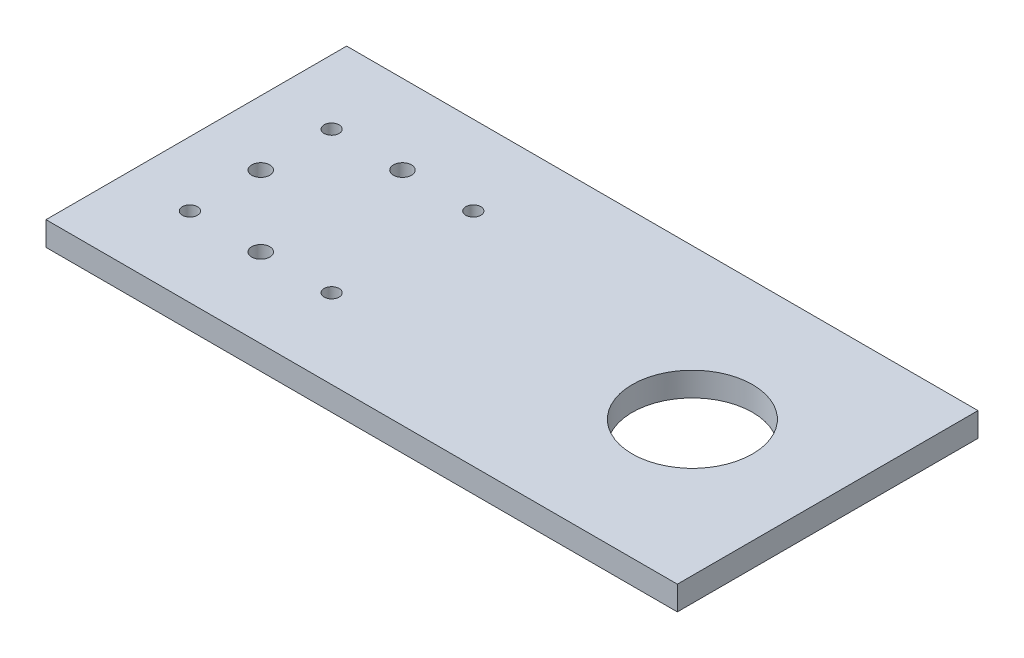
SolidWorks part; units mm, degrees
ref_plane "Front Plane" through (0, 0, 0) normal (0, 0, 1) x (1, 0, 0)
ref_plane "Top Plane" through (0, 0, 0) normal (0, 1, 0) x (1, 0, 0)
ref_plane "Right Plane" through (0, 0, 0) normal (1, 0, 0) x (0, 0, -1)
sketch "Sketch1" plane through (0, 0, 0) normal (0, 1, 0) x (1, 0, 0)
  line L1 (-125, 50) -> (125, 50)
  line L2 (-125, 50) -> (-125, -50)
  line L3 (-125, -50) -> (125, -50)
  line L4 (125, 50) -> (125, -50)
  line L5 (-125, 50) -> (125, -50) construction
  line L6 (-125, -50) -> (125, 50) construction
  point P0 (0, 0)
  dimension "D1" = 100
  dimension "D2" = 250
extrude "Boss-Extrude1" add sketch "Sketch1" along normal blind 8
sketch "Sketch2" plane through (0, 8, 0) normal (0, 1, 0) x (1, 0, 0)
  line L0 (-125, -50) -> (-80, -50)
  line L1 (-125, -50) -> (125, -50) construction
  line L2 (-80, -50) -> (-80, 50)
  line L4 (-116, 36) -> (-44, 36)
  line L5 (-110, 30) -> (-50, 30)
  line L6 (-110, 30) -> (-110, -30)
  line L7 (-110, -30) -> (-50, -30)
  line L8 (-50, 30) -> (-50, -30)
  line L9 (-110, 30) -> (-50, -30) construction
  line L10 (-110, -30) -> (-50, 30) construction
  line L11 (-103.57, 23.57) -> (-56.43, 23.57)
  line L12 (-103.57, 23.57) -> (-103.57, -23.57)
  line L13 (-103.57, -23.57) -> (-56.43, -23.57)
  line L14 (-56.43, 23.57) -> (-56.43, -23.57)
  line L15 (-103.57, 23.57) -> (-56.43, -23.57) construction
  line L16 (-103.57, -23.57) -> (-56.43, 23.57) construction
  line L17 (-116, 36) -> (-116, -36)
  line L18 (-116, -36) -> (-44, -36)
  line L19 (-44, 36) -> (-44, -36)
  line L20 (-116, 36) -> (-44, -36) construction
  line L21 (-116, -36) -> (-44, 36) construction
  circle A0 centre (-80, 0) radius 4
  circle A1 centre (-103.57, 23.57) radius 2.5
  circle A2 centre (-56.43, 23.57) radius 2.5
  circle A3 centre (-56.43, -23.57) radius 2.5
  circle A4 centre (-103.57, -23.57) radius 2.5
  circle A5 centre (-80, 0) radius 19.075
  dimension "D3" = 8
  dimension "D6" = 5
  dimension "D7" = 5
  dimension "D8" = 5
  dimension "D9" = 5
  dimension "D10" = 38.15
  dimension "D2" = 100
  dimension "D4" = 60
  dimension "D5" = 47.14
  dimension "D11" = 45
  dimension "D12" = 72
extrude "Cut-Extrude1" cut sketch "Sketch2" against normal up to surface (8 mm away) contours A1 | A2 | A3 | A4 up to face at (0, 0, 0)
sketch "Sketch3" plane through (0, 8, 0) normal (0, 1, 0) x (1, 0, 0)
  line L0 (-103.57, 23.57) -> (-56.43, 23.57)
  line L1 (-103.57, 23.57) -> (-103.57, -23.57)
  line L2 (-103.57, -23.57) -> (-56.43, -23.57)
  circle A0 centre (-80, 23.57) radius 3
  circle A1 centre (-103.57, 0) radius 3
  circle A2 centre (-80, -23.57) radius 3
  dimension "D1" = 6
  dimension "D2" = 6
  dimension "D3" = 6
extrude "Cut-Extrude2" cut sketch "Sketch3" against normal up to surface (8 mm away) contours A2 | A0 | A1 up to face at (-103.57, 0, 26.07)
sketch "Sketch5" plane through (0, 0, 0) normal (0, -1, 0) x (1, 0, 0)
  line L0 (-125, -50) -> (85, -50)
  line L1 (125, -50) -> (-125, -50) construction
  line L2 (85, -50) -> (85, 50)
  line L3 (-125, 50) -> (125, 50) construction
  line L4 (85, 50) -> (125, 50)
  line L5 (125, 50) -> (125, -50)
  line L6 (125, -50) -> (85, -50)
  dimension "D1" = 210
extrude "Cut-Extrude3" cut sketch "Sketch5" against normal blind 10 contours L2 L4 L5 L6
sketch "Sketch6" plane through (0, 0, 0) normal (0, -1, 0) x (1, 0, 0)
  line L0 (-125, -50) -> (40, -50)
  line L1 (85, -50) -> (-125, -50) construction
  line L2 (40, -50) -> (40, 50)
  line L3 (-125, 50) -> (85, 50) construction
  circle A0 centre (40, 0) radius 20
  dimension "D2" = 40
  dimension "D1" = 165
extrude "Cut-Extrude4" cut sketch "Sketch6" against normal up to surface (8 mm away) contours A0 up to face at (-80, 8, 26.57)
